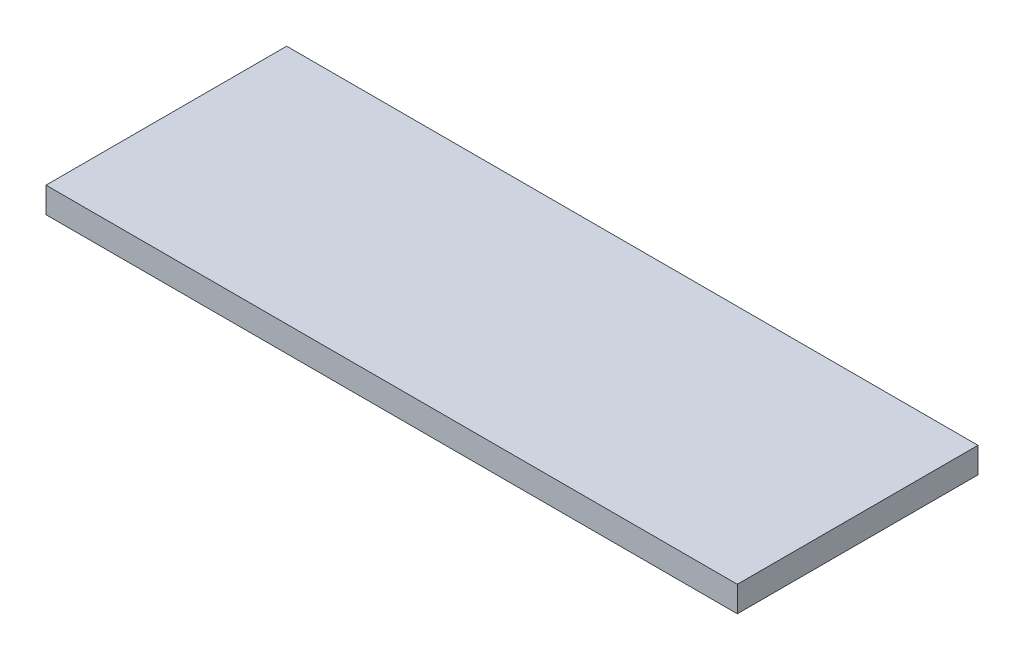
SolidWorks part; units mm, degrees
ref_plane "Front Plane" through (0, 0, 0) normal (0, 0, 1) x (1, 0, 0)
ref_plane "Top Plane" through (0, 0, 0) normal (0, 1, 0) x (1, 0, 0)
ref_plane "Right Plane" through (0, 0, 0) normal (1, 0, 0) x (0, 0, -1)
sketch "Sketch1" plane through (0, 0, 0) normal (0, 1, 0) x (1, 0, 0)
  line L1 (-81, 28.2) -> (81, 28.2)
  line L2 (-81, 28.2) -> (-81, -28.2)
  line L3 (-81, -28.2) -> (81, -28.2)
  line L4 (81, 28.2) -> (81, -28.2)
  line L5 (-81, 28.2) -> (81, -28.2) construction
  line L6 (-81, -28.2) -> (81, 28.2) construction
  point P0 (0, 0)
  dimension "D2" = 56.4
  dimension "D1" = 162
sketch "Sketch2" plane through (0, 0, 0) normal (0, 0, 1) x (1, 0, 0)
  line L0 (0, 0) -> (0, 6) construction
  line L1 (-81, 0) -> (81, 0) construction
  dimension "D1" = 6
extrude "Boss-Extrude1" add sketch "Sketch1" along normal up to vertex (6 mm away) contours L2 L3 L4 L1 up to point (0, 6, 0)
equation "\"glass_width\"= 150"
equation "\"glass_height\"= 100"
equation "\"glass_thickness\"= 4"
equation "\"brood_space\"= 42"
equation "\"t1\"= 6"
equation "\"t2\"= 3.2"
equation "\"box_depth\"= \"brood_space\" + \"glass_thickness\" + \"glass_thickness\" + \"t2\" + \"t2\""
equation "\"box_width\"= \"glass_width\" + \"t1\" + \"t1\""
equation "\"food_height\"= 70"
equation "\"box_height\"= \"glass_height\" + ( \"t1\" * 3 ) + \"food_height\""
equation "\"D1@Sketch1\"=\"box_width\""
equation "\"D2@Sketch1\"=\"box_depth\""
equation "\"D1@Sketch2\"=\"t1\""
